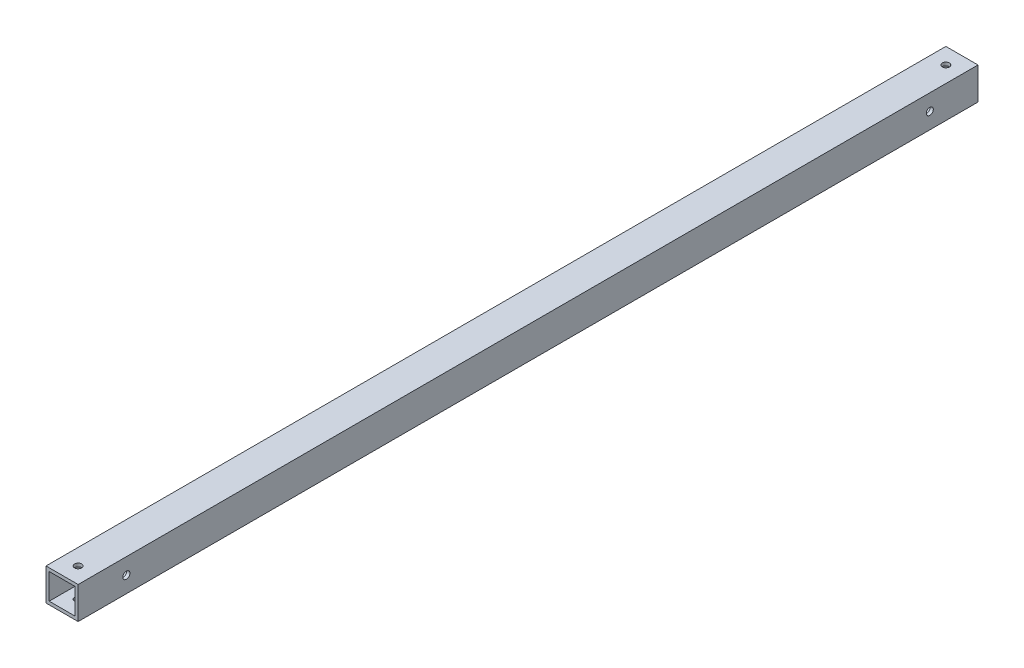
SolidWorks part; units mm, degrees
ref_plane "正面" through (0, 0, 0) normal (0, 0, 1) x (1, 0, 0)
ref_plane "平面" through (0, 0, 0) normal (0, 1, 0) x (1, 0, 0)
ref_plane "右側面" through (0, 0, 0) normal (1, 0, 0) x (0, 0, -1)
sketch "ｽｹｯﾁ1" plane through (0, 0, 0) normal (0, 0, 1) x (1, 0, 0)
  line L1 (-10, 10) -> (10, 10)
  line L2 (-10, 10) -> (-10, -10)
  line L3 (-10, -10) -> (10, -10)
  line L4 (10, 10) -> (10, -10)
  line L5 (-10, 10) -> (10, -10) construction
  line L6 (-10, -10) -> (10, 10) construction
  line L7 (-8, 8) -> (8, 8)
  line L8 (-8, 8) -> (-8, -8)
  line L9 (-8, -8) -> (8, -8)
  line L10 (8, 8) -> (8, -8)
  line L11 (-8, 8) -> (8, -8) construction
  line L12 (-8, -8) -> (8, 8) construction
  point P0 (0, 0)
  point P6 (0, 0)
  dimension "D1" = 20
  dimension "D2" = 20
  dimension "D3" = 16
  dimension "D4" = 16
extrude "ﾎﾞｽ - 押し出し1" add sketch "ｽｹｯﾁ1" along normal blind 560
sketch "ｽｹｯﾁ3" plane through (10, 0, 0) normal (1, 0, 0) x (0, 0, -1)
  line L0 (-560, 0) -> (-530, 0)
  line L1 (-560, -10) -> (-560, 10) construction
  line L2 (-530, 0) -> (-30, 0)
  circle A0 centre (-530, 0) radius 2.2
  circle A1 centre (-30, 0) radius 2.2
  point P8 (0, 0)
  dimension "D2" = 4.4
  dimension "D4" = 4.4
  dimension "D1" = 30
  dimension "D3" = 500
extrude "ｶｯﾄ - 押し出し2" cut sketch "ｽｹｯﾁ3" against normal blind 560
sketch "ｽｹｯﾁ4" plane through (0, 10, 0) normal (0, 1, 0) x (1, 0, 0)
  line L0 (0, -560) -> (0, -550)
  line L1 (10, -560) -> (-10, -560) construction
  line L2 (0, -550) -> (0, -10)
  circle A0 centre (0, -550) radius 2.2
  circle A1 centre (0, -10) radius 2.2
  dimension "D2" = 4.4
  dimension "D4" = 4.4
  dimension "D1" = 10
  dimension "D3" = 540
extrude "ｶｯﾄ - 押し出し3" cut sketch "ｽｹｯﾁ4" against normal blind 560
